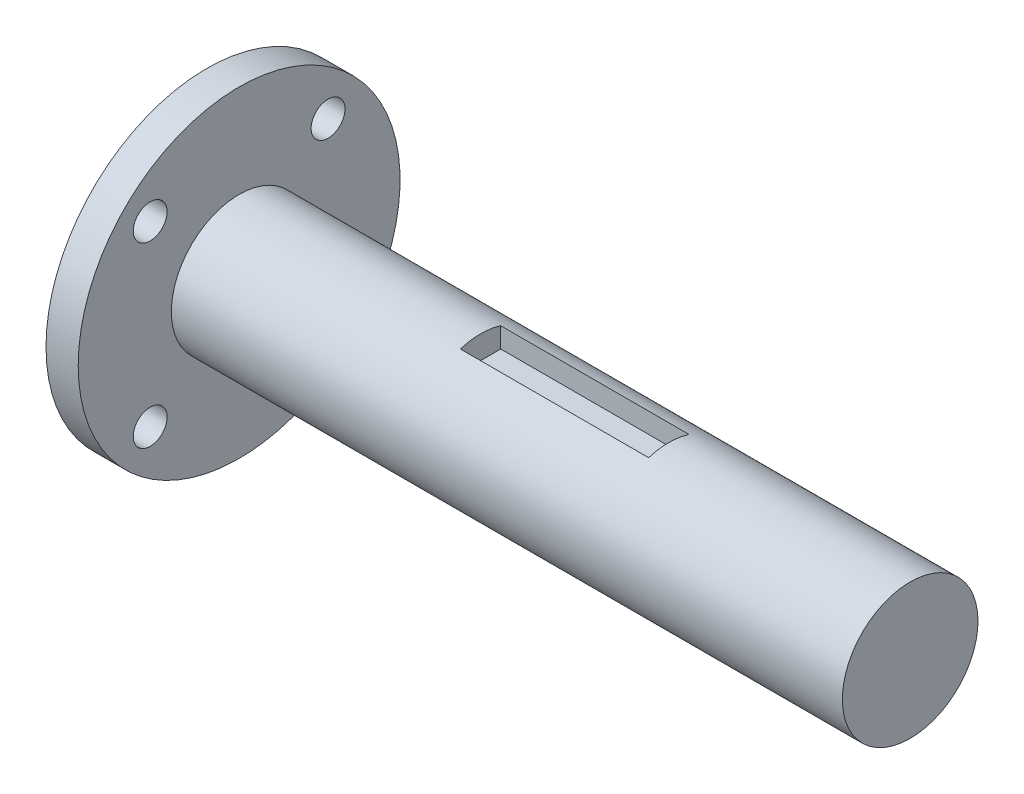
SolidWorks part; units mm, degrees
ref_plane "Piano frontale" through (0, 0, 0) normal (0, 0, 1) x (1, 0, 0)
ref_plane "Piano superiore" through (0, 0, 0) normal (0, 1, 0) x (1, 0, 0)
ref_plane "Piano destro" through (0, 0, 0) normal (1, 0, 0) x (0, 0, -1)
sketch "Sketch1" plane through (0, 0, 0) normal (1, 0, 0) x (0, 0, -1)
  circle A3 centre (0, 0) radius 8.005
  dimension "D1" = 16.01
extrude "Boss-Extrude1" add sketch "Sketch1" along normal blind 28.5
sketch "Sketch4" plane through (0, 0, 0) normal (-1, 0, 0) x (0, 0, 1)
  line L0 (0, 10.5) -> (0, -10.5) construction
  line L1 (-10.5, 10.5) -> (10.5, 10.5) construction
  line L2 (-10.5, 10.5) -> (-10.5, -10.5) construction
  line L3 (-10.5, -10.5) -> (10.5, -10.5) construction
  line L4 (10.5, 10.5) -> (10.5, -10.5) construction
  line L5 (-10.5, 0) -> (10.5, 0) construction
  circle A0 centre (0, 0) radius 19
  circle A1 centre (0, 0) radius 10.75 construction
  circle A4 centre (-10.5, 10.5) radius 2
  circle A5 centre (10.5, 10.5) radius 2
  circle A6 centre (10.5, -10.5) radius 2
  circle A7 centre (-10.5, -10.5) radius 2
  point P23 (0, -10.5)
  point P31 (0, 0)
  dimension "D1" = 38
  dimension "D2" = 4
  dimension "D3" = 21
  dimension "21" = 21
extrude "Boss-Extrude3" add sketch "Sketch4" along normal blind 3.8
sketch "Sketch6" plane through (28.5, 0, 0) normal (1, 0, 0) x (0, 0, -1)
  line L1 (-2.3815, 5.2595) -> (2.3815, 5.2595)
  line L2 (-2.3815, 5.2595) -> (-2.3815, 7.6425)
  line L4 (2.3815, 5.2595) -> (2.3815, 7.6425)
  arc A0 (-2.3815, 7.6425) -> (2.3815, 7.6425) centre (0, 0) ccw
  point P7 (0, 5.2595)
  dimension "D3" = 16.01
  dimension "D1" = 2.383
  dimension "D2" = 4.763
extrude "Boss-Extrude5" add sketch "Sketch6" along normal blind 22.225
sketch "Sketch7" plane through (50.725, 0, 0) normal (1, 0, 0) x (0, 0, -1)
  circle A0 centre (0, 0) radius 8.005
  dimension "D1" = 16.01
extrude "Boss-Extrude6" add sketch "Sketch7" along normal blind 28.5
